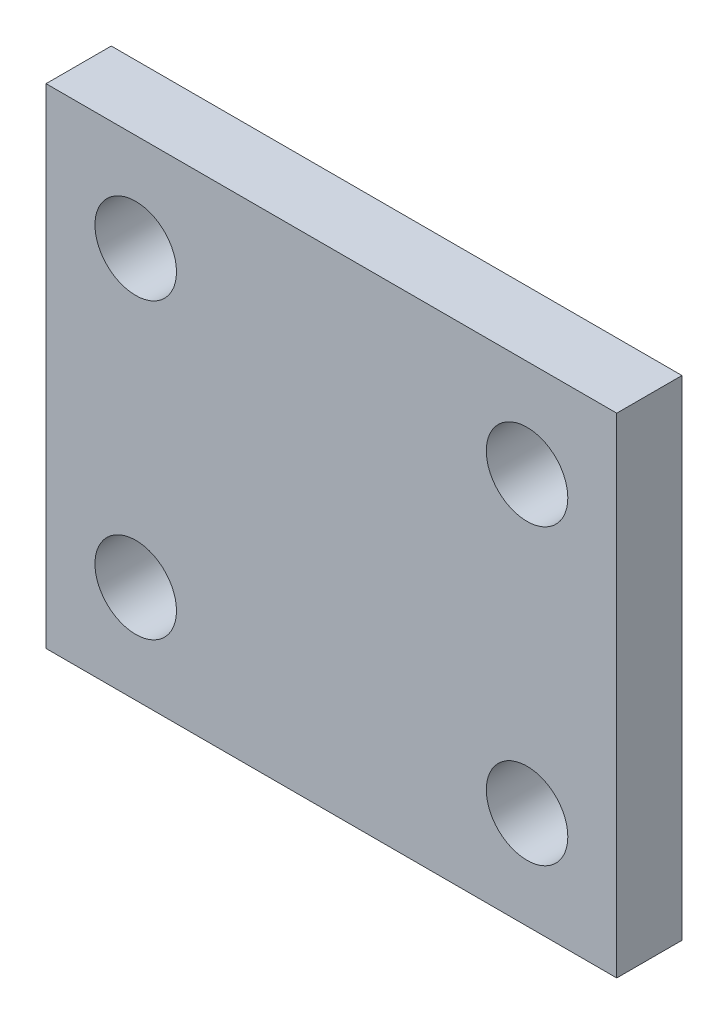
SolidWorks part; units mm, degrees
ref_plane "Front Plane" through (0, 0, 0) normal (0, 0, 1) x (1, 0, 0)
ref_plane "Top Plane" through (0, 0, 0) normal (0, 1, 0) x (1, 0, 0)
ref_plane "Right Plane" through (0, 0, 0) normal (1, 0, 0) x (0, 0, -1)
sketch "Sketch1" plane through (0, 0, 0) normal (0, 0, 1) x (1, 0, 0)
  line L1 (0, 0) -> (35, 0)
  line L2 (0, 0) -> (0, 30)
  line L3 (0, 30) -> (35, 30)
  line L4 (35, 0) -> (35, 30)
  circle A0 centre (5.5, 24) radius 2.5
  circle A1 centre (29.5, 24) radius 2.5
  circle A2 centre (5.5, 6) radius 2.5
  circle A3 centre (29.5, 6) radius 2.5
extrude "Boss-Extrude1" add sketch "Sketch1" along normal blind 4
